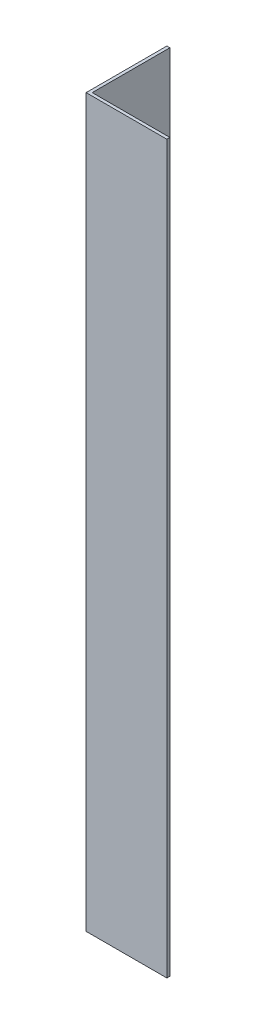
SolidWorks part; units mm, degrees
material "1060 Сплав"
ref_plane "Спереди" through (0, 0, 0) normal (0, 0, 1) x (1, 0, 0)
ref_plane "Сверху" through (0, 0, 0) normal (0, 1, 0) x (1, 0, 0)
ref_plane "Справа" through (0, 0, 0) normal (1, 0, 0) x (0, 0, -1)
sketch "Эскиз1" plane through (0, 0, 0) normal (0, 1, 0) x (1, 0, 0)
  line L0 (0, 0) -> (0, 20)
  line L1 (0, 20) -> (0.75, 20)
  line L2 (0.75, 20) -> (0.75, 0.75)
  line L3 (0.75, 0.75) -> (20, 0.75)
  line L4 (20, 0.75) -> (20, 0)
  line L5 (20, 0) -> (0, 0)
  dimension "D1" = 0.75
  dimension "D2" = 20
extrude "Бобышка-Вытянуть1" add sketch "Эскиз1" along normal blind 180
